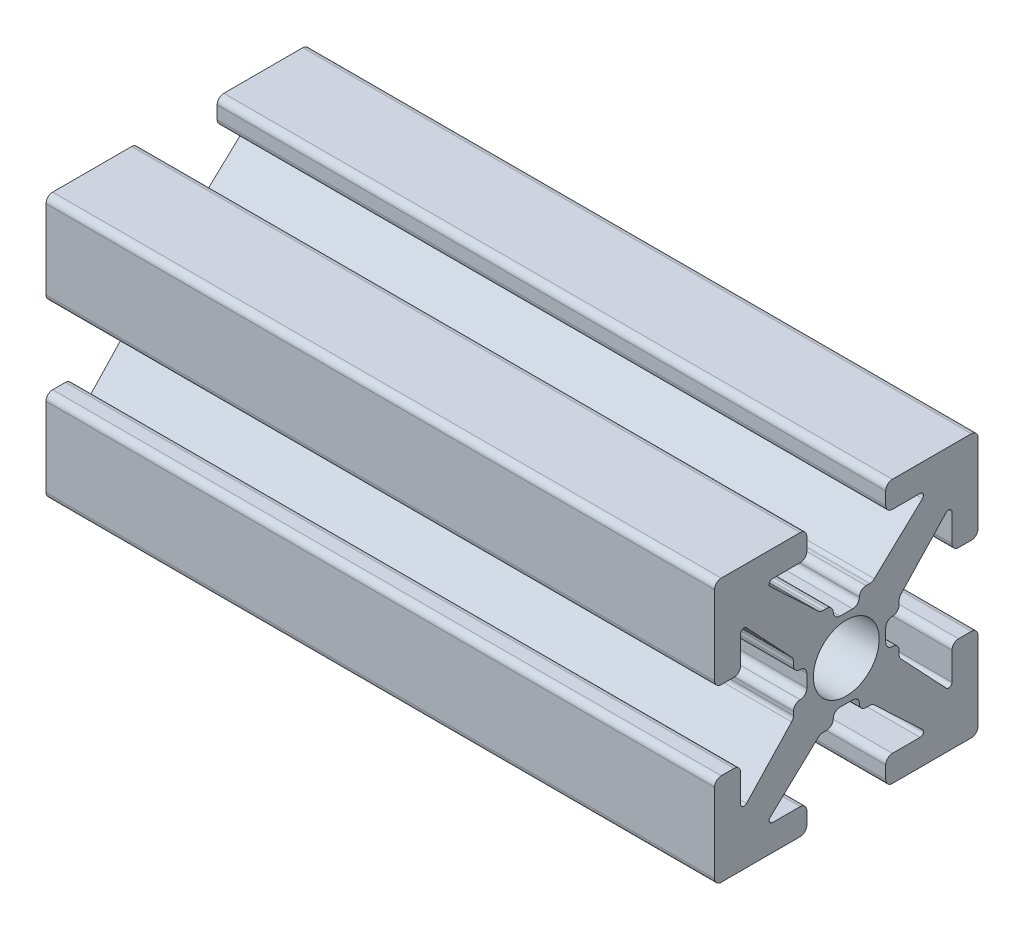
SolidWorks part; units mm, degrees
material "Acciaio in lega fuso"
ref_plane "Front Plane" through (0, 0, 0) normal (0, 0, 1) x (1, 0, 0)
ref_plane "Top Plane" through (0, 0, 0) normal (0, 1, 0) x (1, 0, 0)
ref_plane "Right Plane" through (0, 0, 0) normal (1, 0, 0) x (0, 0, -1)
sketch "Sketch1" plane through (0, 0, 0) normal (1, 0, 0) x (0, 0, -1)
  line L0 (0, 0) -> (0, 1.4986) construction
  line L1 (-0.2413, 1.4986) -> (0.2413, 1.4986)
  line L2 (5.0038, 1.7526) -> (5.0038, 4.7498)
  line L3 (0.7493, 2.0066) -> (0.8899, 2.0066)
  line L4 (1.0639, 2.0756) -> (2.8908, 3.7937)
  line L5 (2.8038, 4.0132) -> (1.7526, 4.0132)
  line L6 (1.4986, 4.2672) -> (1.4986, 4.7498)
  line L7 (1.7526, 5.0038) -> (4.7498, 5.0038)
  line L8 (5.0038, 5.0038) -> (0, 0) construction
  line L9 (0, 0) -> (8.6271, 0) construction
  line L10 (0, 0) -> (0, 5.0038) construction
  line L11 (4.2672, 1.4986) -> (4.7498, 1.4986)
  line L12 (4.0132, 2.8038) -> (4.0132, 1.7526)
  line L13 (2.0756, 1.0639) -> (3.7937, 2.8908)
  line L14 (2.0066, 0.7493) -> (2.0066, 0.8899)
  line L15 (1.4986, -0.2413) -> (1.4986, 0.2413)
  line L16 (0, 0) -> (1.4986, 0) construction
  line L17 (-0.2413, -1.4986) -> (0.2413, -1.4986)
  line L18 (0.7493, -2.0066) -> (0.8899, -2.0066)
  line L19 (1.0639, -2.0756) -> (2.8908, -3.7937)
  line L20 (2.8038, -4.0132) -> (1.7526, -4.0132)
  line L21 (1.4986, -4.2672) -> (1.4986, -4.7498)
  line L22 (1.7526, -5.0038) -> (4.7498, -5.0038)
  line L23 (5.0038, -1.7526) -> (5.0038, -4.7498)
  line L24 (4.2672, -1.4986) -> (4.7498, -1.4986)
  line L25 (4.0132, -2.8038) -> (4.0132, -1.7526)
  line L26 (2.0756, -1.0639) -> (3.7937, -2.8908)
  line L27 (2.0066, -0.7493) -> (2.0066, -0.8899)
  line L28 (-0.7493, 2.0066) -> (-0.8899, 2.0066)
  line L29 (-1.0639, 2.0756) -> (-2.8908, 3.7937)
  line L30 (-2.8038, 4.0132) -> (-1.7526, 4.0132)
  line L31 (-1.4986, 4.2672) -> (-1.4986, 4.7498)
  line L32 (-1.7526, 5.0038) -> (-4.7498, 5.0038)
  line L33 (-5.0038, 1.7526) -> (-5.0038, 4.7498)
  line L34 (-4.2672, 1.4986) -> (-4.7498, 1.4986)
  line L35 (-4.0132, 2.8038) -> (-4.0132, 1.7526)
  line L36 (-2.0756, 1.0639) -> (-3.7937, 2.8908)
  line L37 (-2.0066, 0.7493) -> (-2.0066, 0.8899)
  line L38 (-1.4986, -0.2413) -> (-1.4986, 0.2413)
  line L39 (-2.0066, -0.7493) -> (-2.0066, -0.8899)
  line L40 (-2.0756, -1.0639) -> (-3.7937, -2.8908)
  line L41 (-4.0132, -2.8038) -> (-4.0132, -1.7526)
  line L42 (-4.2672, -1.4986) -> (-4.7498, -1.4986)
  line L43 (-5.0038, -1.7526) -> (-5.0038, -4.7498)
  line L44 (-1.7526, -5.0038) -> (-4.7498, -5.0038)
  line L45 (-1.4986, -4.2672) -> (-1.4986, -4.7498)
  line L46 (-2.8038, -4.0132) -> (-1.7526, -4.0132)
  line L47 (-1.0639, -2.0756) -> (-2.8908, -3.7937)
  line L48 (-0.7493, -2.0066) -> (-0.8899, -2.0066)
  arc A0 (2.8908, 3.7937) -> (2.8038, 4.0132) centre (2.8038, 3.8862) ccw
  arc A1 (0.4953, 1.7526) -> (0.7493, 2.0066) centre (0.7493, 1.7526) cw
  arc A2 (0.8899, 2.0066) -> (1.0639, 2.0756) centre (0.8899, 2.2606) ccw
  arc A3 (1.7526, 4.0132) -> (1.4986, 4.2672) centre (1.7526, 4.2672) cw
  arc A4 (1.4986, 4.7498) -> (1.7526, 5.0038) centre (1.7526, 4.7498) cw
  arc A5 (0.2413, 1.4986) -> (0.4953, 1.7526) centre (0.2413, 1.7526) ccw
  arc A6 (4.7498, 1.4986) -> (5.0038, 1.7526) centre (4.7498, 1.7526) ccw
  arc A7 (4.0132, 1.7526) -> (4.2672, 1.4986) centre (4.2672, 1.7526) ccw
  arc A8 (3.7937, 2.8908) -> (4.0132, 2.8038) centre (3.8862, 2.8038) cw
  arc A9 (2.0066, 0.8899) -> (2.0756, 1.0639) centre (2.2606, 0.8899) cw
  arc A10 (1.7526, 0.4953) -> (2.0066, 0.7493) centre (1.7526, 0.7493) ccw
  arc A11 (1.4986, 0.2413) -> (1.7526, 0.4953) centre (1.7526, 0.2413) cw
  arc A12 (0.2413, -1.4986) -> (0.4953, -1.7526) centre (0.2413, -1.7526) cw
  arc A13 (0.4953, -1.7526) -> (0.7493, -2.0066) centre (0.7493, -1.7526) ccw
  arc A14 (0.8899, -2.0066) -> (1.0639, -2.0756) centre (0.8899, -2.2606) cw
  arc A15 (2.8908, -3.7937) -> (2.8038, -4.0132) centre (2.8038, -3.8862) cw
  arc A16 (1.7526, -4.0132) -> (1.4986, -4.2672) centre (1.7526, -4.2672) ccw
  arc A17 (1.4986, -4.7498) -> (1.7526, -5.0038) centre (1.7526, -4.7498) ccw
  arc A18 (4.7498, -1.4986) -> (5.0038, -1.7526) centre (4.7498, -1.7526) cw
  arc A19 (4.0132, -1.7526) -> (4.2672, -1.4986) centre (4.2672, -1.7526) cw
  arc A20 (3.7937, -2.8908) -> (4.0132, -2.8038) centre (3.8862, -2.8038) ccw
  arc A21 (2.0066, -0.8899) -> (2.0756, -1.0639) centre (2.2606, -0.8899) ccw
  arc A22 (1.7526, -0.4953) -> (2.0066, -0.7493) centre (1.7526, -0.7493) cw
  arc A23 (1.4986, -0.2413) -> (1.7526, -0.4953) centre (1.7526, -0.2413) ccw
  arc A24 (-0.2413, 1.4986) -> (-0.4953, 1.7526) centre (-0.2413, 1.7526) cw
  arc A25 (-0.4953, 1.7526) -> (-0.7493, 2.0066) centre (-0.7493, 1.7526) ccw
  arc A26 (-0.8899, 2.0066) -> (-1.0639, 2.0756) centre (-0.8899, 2.2606) cw
  arc A27 (-2.8908, 3.7937) -> (-2.8038, 4.0132) centre (-2.8038, 3.8862) cw
  arc A28 (-1.7526, 4.0132) -> (-1.4986, 4.2672) centre (-1.7526, 4.2672) ccw
  arc A29 (-1.4986, 4.7498) -> (-1.7526, 5.0038) centre (-1.7526, 4.7498) ccw
  arc A30 (-4.7498, 1.4986) -> (-5.0038, 1.7526) centre (-4.7498, 1.7526) cw
  arc A31 (-4.0132, 1.7526) -> (-4.2672, 1.4986) centre (-4.2672, 1.7526) cw
  arc A32 (-3.7937, 2.8908) -> (-4.0132, 2.8038) centre (-3.8862, 2.8038) ccw
  arc A33 (-2.0066, 0.8899) -> (-2.0756, 1.0639) centre (-2.2606, 0.8899) ccw
  arc A34 (-1.7526, 0.4953) -> (-2.0066, 0.7493) centre (-1.7526, 0.7493) cw
  arc A35 (-1.4986, 0.2413) -> (-1.7526, 0.4953) centre (-1.7526, 0.2413) ccw
  arc A36 (-1.4986, -0.2413) -> (-1.7526, -0.4953) centre (-1.7526, -0.2413) cw
  arc A37 (-1.7526, -0.4953) -> (-2.0066, -0.7493) centre (-1.7526, -0.7493) ccw
  arc A38 (-2.0066, -0.8899) -> (-2.0756, -1.0639) centre (-2.2606, -0.8899) cw
  arc A39 (-3.7937, -2.8908) -> (-4.0132, -2.8038) centre (-3.8862, -2.8038) cw
  arc A40 (-4.0132, -1.7526) -> (-4.2672, -1.4986) centre (-4.2672, -1.7526) ccw
  arc A41 (-4.7498, -1.4986) -> (-5.0038, -1.7526) centre (-4.7498, -1.7526) ccw
  arc A42 (-1.4986, -4.7498) -> (-1.7526, -5.0038) centre (-1.7526, -4.7498) cw
  arc A43 (-1.7526, -4.0132) -> (-1.4986, -4.2672) centre (-1.7526, -4.2672) cw
  arc A44 (-2.8908, -3.7937) -> (-2.8038, -4.0132) centre (-2.8038, -3.8862) ccw
  arc A45 (-0.8899, -2.0066) -> (-1.0639, -2.0756) centre (-0.8899, -2.2606) ccw
  arc A46 (-0.4953, -1.7526) -> (-0.7493, -2.0066) centre (-0.7493, -1.7526) cw
  arc A47 (-0.2413, -1.4986) -> (-0.4953, -1.7526) centre (-0.2413, -1.7526) ccw
  arc A48 (-4.7498, 5.0038) -> (-5.0038, 4.7498) centre (-4.7498, 4.7498) ccw
  arc A49 (-5.0038, -4.7498) -> (-4.7498, -5.0038) centre (-4.7498, -4.7498) ccw
  arc A50 (4.7498, -5.0038) -> (5.0038, -4.7498) centre (4.7498, -4.7498) ccw
  arc A51 (4.7498, 5.0038) -> (5.0038, 4.7498) centre (4.7498, 4.7498) cw
  point P14 (3.1242, 4.0132)
  point P19 (0.9906, 2.0066)
  point P150 (0, -1.4986)
  point P152 (-5.0038, 5.0038)
  point P155 (-5.0038, -5.0038)
  point P158 (5.0038, -5.0038)
  dimension "D10" = 0.127
  dimension "D11" = 0.254
  dimension "D2" = 0.254
  dimension "D1" = 10.0076
  dimension "D3" = 2.9972
  dimension "D4" = 0.508
  dimension "D5" = 2.9972
  dimension "D6" = 0.9906
  dimension "D7" = 1.6256
  dimension "D8" = 1.9812
  dimension "D9" = 0.9906
extrude "Estrusione-Estrusione1" add sketch "Sketch1" along normal blind 25.4 contours L36 A32 L35 A31 L34 A30 L33 A48 L32 A29 L31 A28 L30 A27 L29 A26 L28 A25 A24 L1 A5 A1 L3 A2 L4 A0 L5 A3 L6 A4 L7 A51 L2 A6 L11 A7 L12 A8 L13 A9 L14 A10 A11 L15 A23 A22 L27 A21 L26 A20 L25 A19 L24 A18 L23 A50 L22 A17 L21 A16 L20 A15 L19 A14 L18 A13 A12 L17 A47 A46 L48 A45 L47 A44 L46 A43 L45 A42 L44 A49 L43 A41 L42 A40 L41 A39 L40 A38 L39 A37 A36 L38 A35 A34 L37 A33
hole_wizard "Foro filettato M3x0.5-1" positions "Schizzo2" profile "Schizzo1" tap size "M3x0.5" standard "Ansi Metric" end condition through all
sketch "Schizzo2" plane through (0, 0, 0) normal (-1, 0, 0) x (0, 0, 1)
  point P0 (0, 0)
sketch "Schizzo1" plane through (0, 0, 0) normal (0, 1, 0) x (0, 0, 1)
  line L0 (0, 0) -> (0, 25.4)
  line L1 (0, 25.4) -> (1.25, 25.4)
  line L2 (1.25, 25.4) -> (1.25, 0)
  line L5 (1.25, 0) -> (0, 0)
  line L11 (0, -6.35) -> (0, 107.95) construction
  dimension "Thread Major Dia." = 2.5
  dimension "Thru Tap Drill Depth" = 25.4
